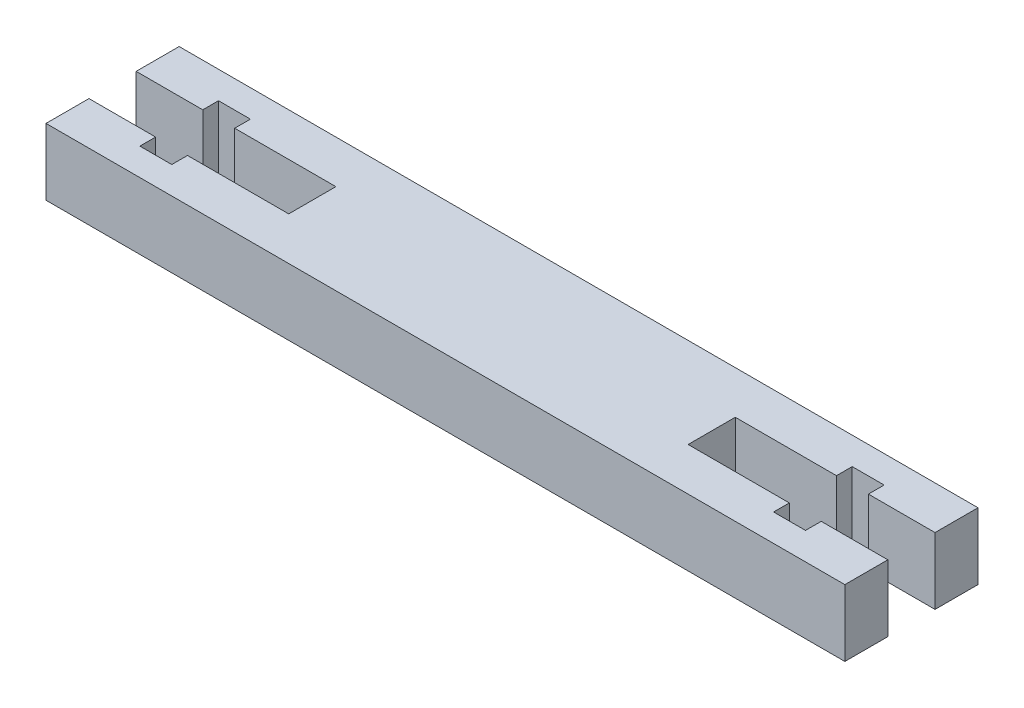
SolidWorks part; units mm, degrees
ref_plane "Front Plane" through (0, 0, 0) normal (0, 0, 1) x (1, 0, 0)
ref_plane "Top Plane" through (0, 0, 0) normal (0, 1, 0) x (1, 0, 0)
ref_plane "Right Plane" through (0, 0, 0) normal (1, 0, 0) x (0, 0, -1)
sketch "Sketch1" plane through (0, 0, 0) normal (0, 1, 0) x (1, 0, 0)
  line L1 (0, 0) -> (76.2, 0)
  line L2 (0, 0) -> (0, -12.7)
  line L3 (0, -12.7) -> (76.2, -12.7)
  line L4 (76.2, 0) -> (76.2, -12.7)
extrude "Boss-Extrude1" add sketch "Sketch1" along normal blind 6.35
sketch "Sketch2" plane through (0, 0, 0) normal (0, -1, 0) x (-1, 0, 0)
  line L0 (-68.3239, -6.35) -> (-68.3239, -10.1) construction
  line L1 (-76.2, -6.35) -> (-69.8459, -6.35) construction
  line L4 (-68.3239, -2.6) -> (-68.3239, -6.35) construction
  line L5 (-69.8459, -6.35) -> (-57.1495, -6.35) construction
  line L6 (-76.2, -8.6) -> (-76.2, -4.1)
  line L8 (-76.2, -4.1) -> (-69.8459, -4.1)
  line L15 (-76.2, -8.6) -> (-69.8459, -8.6)
  line L19 (-38.1, -12.7) -> (-38.1, 0) construction
  line L20 (0, -12.7) -> (-76.2, -12.7) construction
  line L21 (-43.1, 0) -> (-33.1, 0) construction
  line L22 (-6.3541, -6.35) -> (-19.0505, -6.35) construction
  line L23 (-7.8761, -2.6) -> (-7.8761, -6.35) construction
  line L24 (0, -6.35) -> (-6.3541, -6.35) construction
  line L25 (-7.8761, -6.35) -> (-7.8761, -10.1) construction
  line L26 (-19.0505, -4.1) -> (-9.398, -4.1)
  line L27 (-19.0505, -8.6) -> (-19.0505, -4.1)
  line L28 (-9.398, -8.6) -> (-19.0505, -8.6)
  line L29 (-9.398, -2.6) -> (-9.398, -4.1)
  line L30 (-6.3541, -2.6) -> (-9.398, -2.6)
  line L31 (-9.398, -10.1) -> (-9.398, -8.6)
  line L32 (-6.3541, -10.1) -> (-9.398, -10.1)
  line L33 (-6.3541, -4.1) -> (-6.3541, -2.6)
  line L34 (-6.3541, -8.6) -> (-6.3541, -10.1)
  line L35 (0, -8.6) -> (-6.3541, -8.6)
  line L36 (0, -4.1) -> (-6.3541, -4.1)
  line L37 (0, -8.6) -> (0, -4.1)
  line L38 (-69.8459, -8.6) -> (-69.8459, -10.1)
  line L39 (-69.8459, -4.1) -> (-69.8459, -2.6)
  line L40 (-69.8459, -10.1) -> (-66.802, -10.1)
  line L41 (-66.802, -10.1) -> (-66.802, -8.6)
  line L42 (-69.8459, -2.6) -> (-66.802, -2.6)
  line L43 (-66.802, -2.6) -> (-66.802, -4.1)
  line L44 (-66.802, -8.6) -> (-57.1495, -8.6)
  line L45 (-57.1495, -8.6) -> (-57.1495, -4.1)
  line L46 (-57.1495, -4.1) -> (-66.802, -4.1)
  point P0 (0, 0)
  point P45 (0, 0)
  point P46 (0, 0)
extrude "Cut-Extrude1" cut sketch "Sketch2" against normal through all and the other way through all
